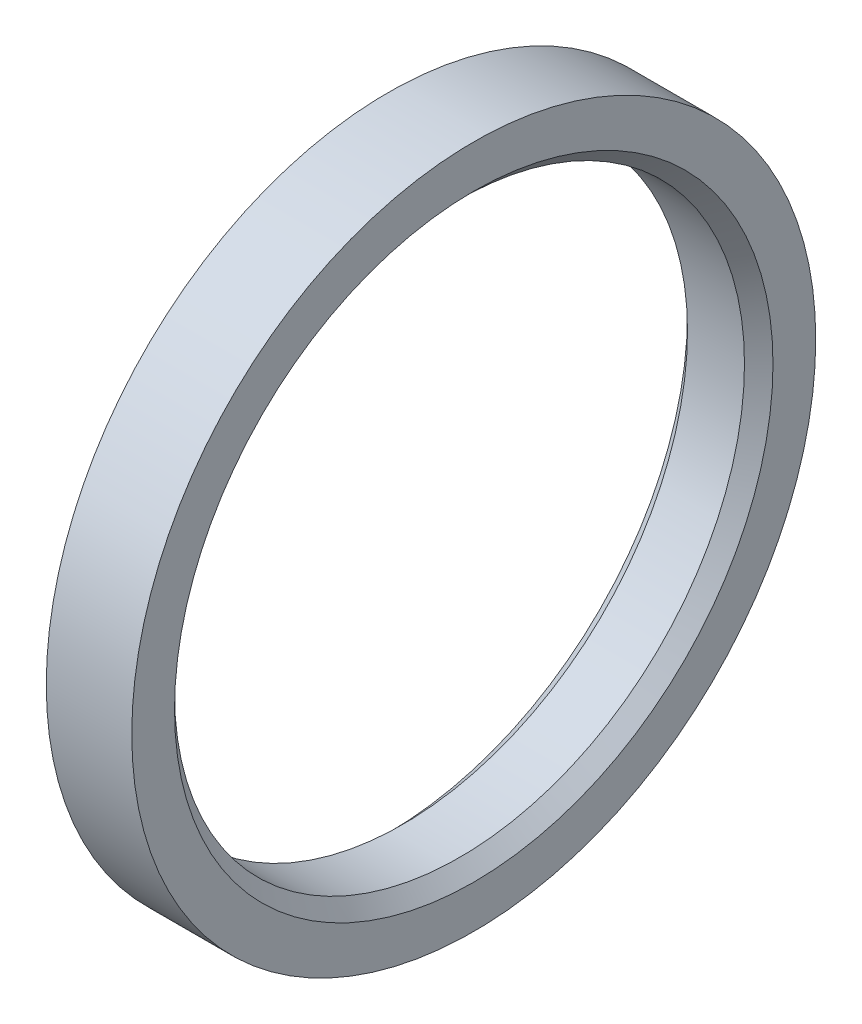
SolidWorks part; units mm, degrees
material "Сталь ШХ15 ГОСТ 801-78"
ref_plane "Plane1" through (0, 0, 0) normal (0, 0, 1) x (1, 0, 0)
ref_plane "Plane2" through (0, 0, 0) normal (0, 1, 0) x (1, 0, 0)
ref_plane "Plane3" through (0, 0, 0) normal (1, 0, 0) x (0, 0, -1)
sketch "Эскиз1" plane through (0, 0, 0) normal (0, 0, 1) x (1, 0, 0)
  line L0 (0, 0) -> (-23.442, 0) construction
  line L2 (0, 10) -> (3, 10)
  line L3 (0, 10) -> (0, 12)
  line L4 (0, 12) -> (3, 12)
  line L5 (3, 10) -> (3, 12)
  dimension "D1" = 20
  dimension "D2" = 24
  dimension "D3" = 3
revolve "Повернуть1" add sketch "Эскиз1" angle 360 about L0
chamfer "Фаска1" distance 0.5 angle 45 2 edges at (0, 0, -10) (3, 0, -10)
